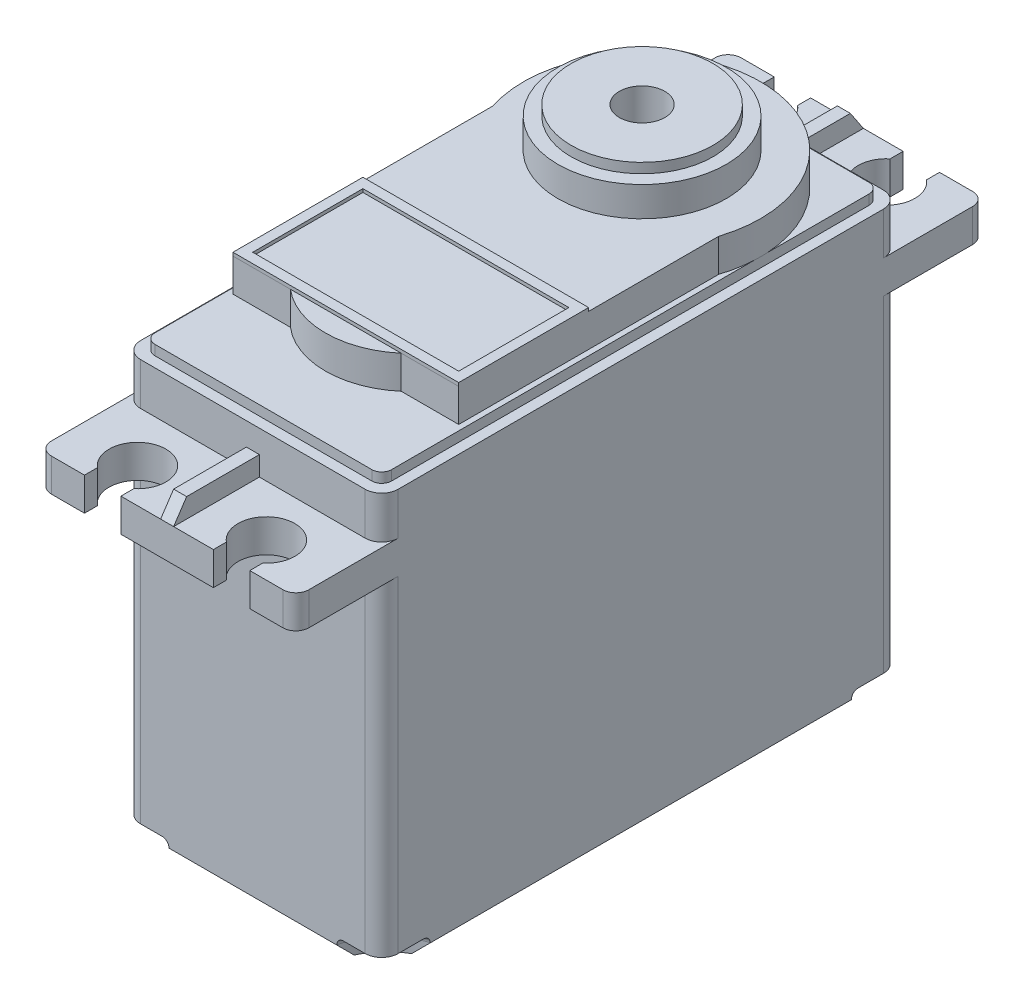
SolidWorks part; units mm, degrees
material "PBT General Purpose"
ref_plane "Front Plane" through (0, 0, 0) normal (0, 0, 1) x (1, 0, 0)
ref_plane "Top Plane" through (0, 0, 0) normal (0, 1, 0) x (1, 0, 0)
ref_plane "Right Plane" through (0, 0, 0) normal (1, 0, 0) x (0, 0, -1)
sketch "Sketch1" plane through (0, 0, 0) normal (0, 1, 0) x (1, 0, 0)
  line L0 (0, 19.94) -> (0, -19.94) construction
  line L1 (9.91, -19.94) -> (-9.91, -19.94)
  line L2 (9.91, -19.94) -> (9.91, 19.94)
  line L3 (9.91, 19.94) -> (-9.91, 19.94)
  line L4 (-9.91, -19.94) -> (-9.91, 19.94)
  line L5 (-9.91, 0) -> (9.91, 0) construction
  point P0 (0, 0)
  dimension "D1" = 19.82
  dimension "D2" = 39.88
extrude "Boss-Extrude1" add sketch "Sketch1" along normal blind 36.02
ref_plane "Plane1" through (0, 26.67, 0) normal (0, 1, 0) x (1, 0, 0)
sketch "Sketch2" plane through (0, 26.67, 0) normal (0, 1, 0) x (1, 0, 0)
  line L0 (0, 19.94) -> (0, -19.94) construction
  line L1 (9.91, 19.94) -> (-9.91, 19.94) construction
  line L2 (-9.91, -19.94) -> (9.91, -19.94) construction
  line L3 (-9.91, 0) -> (9.91, 0) construction
  line L4 (-9.91, 19.94) -> (-9.91, -19.94) construction
  line L5 (9.91, -19.94) -> (9.91, 19.94) construction
  line L7 (-9.91, 19.94) -> (9.91, 19.94)
  line L8 (-9.91, 19.94) -> (-9.91, 26.54)
  line L9 (-9.91, 26.54) -> (9.91, 26.54)
  line L10 (9.91, 19.94) -> (9.91, 26.54)
  line L11 (-9.91, -19.94) -> (9.91, -19.94)
  line L12 (-9.91, -19.94) -> (-9.91, -26.54)
  line L13 (-9.91, -26.54) -> (9.91, -26.54)
  line L14 (9.91, -19.94) -> (9.91, -26.54)
  dimension "D1" = 6.6
extrude "Boss-Extrude2" add sketch "Sketch2" along normal blind 2.54
ref_plane "Plane2" through (0, 29.21, 0) normal (0, 1, 0) x (1, 0, 0)
sketch "Sketch3" plane through (0, 29.21, 0) normal (0, 1, 0) x (1, 0, 0)
  line L0 (0, 26.54) -> (0, -26.54) construction
  line L1 (9.91, 26.54) -> (-9.91, 26.54) construction
  line L2 (-9.91, -26.54) -> (9.91, -26.54) construction
  line L3 (-4.96, 26.54) -> (-4.96, -26.54) construction
  line L4 (-6.36, 26.54) -> (-3.56, 26.54)
  line L5 (-6.36, 26.54) -> (-6.36, 25.54)
  line L6 (-3.56, 26.54) -> (-3.56, 25.54)
  line L7 (3.56, 26.54) -> (3.56, 25.54)
  line L8 (6.36, 26.54) -> (6.36, 25.54)
  line L9 (6.36, 26.54) -> (3.56, 26.54)
  arc A0 (-6.36, 25.5441) -> (-3.56, 25.5441) centre (-4.96, 23.86) ccw
  arc A1 (6.36, 25.5441) -> (3.56, 25.5441) centre (4.96, 23.86) cw
  point P11 (-4.96, 26.54)
  point P24 (4.96, 26.54)
  dimension "D5" = 2.19
  dimension "D1" = 4.96
  dimension "D2" = 2.8
  dimension "D3" = 1
  dimension "D4" = 23.86
extrude "Cut-Extrude1" cut sketch "Sketch3" along direction (0, -1, 0) on the side against the normal blind 2.54
mirror "Mirror1" about plane through (0, 0, 0) normal (0, 0, 1) of "Cut-Extrude1"
ref_plane "Plane3" through (0, 29.21, 0) normal (0, 1, 0) x (1, 0, 0)
sketch "Sketch4" plane through (0, 29.21, 0) normal (0, 1, 0) x (1, 0, 0)
  line L0 (0, 26.54) -> (0, -26.54) construction
  line L1 (3.56, 26.54) -> (-3.56, 26.54) construction
  line L2 (-3.56, -26.54) -> (3.56, -26.54) construction
  line L3 (-9.91, 0) -> (9.91, 0) construction
  line L4 (-9.91, 19.94) -> (-9.91, -19.94) construction
  line L5 (9.91, -19.94) -> (9.91, 19.94) construction
  line L6 (-9.91, 19.94) -> (9.91, 19.94) construction
  line L7 (-0.5, 26.54) -> (0.5, 26.54)
  line L8 (-0.5, 26.54) -> (-0.5, 19.94)
  line L9 (-0.5, 19.94) -> (0.5, 19.94)
  line L10 (0.5, 26.54) -> (0.5, 19.94)
  line L11 (0.5, -26.54) -> (0.5, -19.94)
  line L12 (-0.5, -19.94) -> (0.5, -19.94)
  line L13 (-0.5, -26.54) -> (-0.5, -19.94)
  line L14 (-0.5, -26.54) -> (0.5, -26.54)
  point P18 (0, 26.54)
  dimension "D1" = 1
extrude "Boss-Extrude3" add sketch "Sketch4" along normal blind 1.5
ref_plane "Plane4" through (-0.5, 0, 0) normal (-1, 0, 0) x (0, 0, 1)
sketch "Sketch5" plane through (-0.5, 0, 0) normal (-1, 0, 0) x (0, 0, 1)
  line L0 (0, 36.02) -> (0, 0) construction
  line L1 (-19.94, 36.02) -> (19.94, 36.02) construction
  line L2 (-26.54, 30.71) -> (-25.54, 30.71)
  line L3 (-26.54, 30.71) -> (-19.94, 30.71) construction
  line L4 (-26.54, 30.71) -> (-26.54, 29.21)
  line L5 (-25.54, 30.71) -> (-26.54, 29.21)
  line L6 (25.54, 30.71) -> (26.54, 29.21)
  line L7 (26.54, 30.71) -> (26.54, 29.21)
  line L8 (26.54, 30.71) -> (25.54, 30.71)
  dimension "D1" = 1
extrude "Cut-Extrude2" cut sketch "Sketch5" against normal through all both and the other way through all
ref_plane "Plane5" through (0, 36.02, 0) normal (0, 1, 0) x (1, 0, 0)
sketch "Sketch6" plane through (0, 36.02, 0) normal (0, 1, 0) x (1, 0, 0)
  line L1 (-9.91, 19.94) -> (9.91, 19.94)
  line L2 (-9.91, 19.94) -> (-9.91, -19.94)
  line L3 (-9.91, -19.94) -> (9.91, -19.94)
  line L4 (9.91, 19.94) -> (9.91, -19.94)
extrude "Cut-Extrude3" cut sketch "Sketch6" against normal blind 3.55
ref_plane "Plane6" through (0, 32.47, 0) normal (0, 1, 0) x (1, 0, 0)
sketch "Sketch7" plane through (0, 32.47, 0) normal (0, 1, 0) x (1, 0, 0)
  line L0 (0, 19.94) -> (0, -19.94) construction
  line L5 (-9.91, 0) -> (9.91, 0) construction
  line L18 (-9.11, 19.136) -> (-9.11, -19.136)
  line L19 (9.11, 19.136) -> (9.11, -19.136)
  line L20 (-9.11, 19.136) -> (9.11, 19.136)
  line L21 (-9.11, -19.136) -> (9.11, -19.136)
  line L22 (-0.5, -19.94) -> (-9.91, -19.94) construction
  line L23 (-9.91, 19.94) -> (-0.5, 19.94) construction
  line L24 (-9.91, 19.94) -> (-9.91, -19.94) construction
  point P7 (-9.11, 0)
  point P10 (9.11, 0)
  dimension "D1" = 18.22
  dimension "D2" = 0.804
  dimension "D3" = 0.804
  dimension "D4" = 0.8
extrude "Boss-Extrude4" add sketch "Sketch7" along normal blind 0.762
fillet "Fillet1" radius 1.27 8 edges at (-9.91, 30.84, 19.94) (-9.91, 13.335, 19.94) (-9.91, 30.84, -19.94) (-9.91, 13.335, -19.94) (9.91, 30.84, -19.94) (9.91, 13.335, -19.94) (9.91, 30.84, 19.94) (9.91, 13.335, 19.94)
fillet "Fillet2" radius 0.762 4 edges at (-9.11, 32.851, -19.136) (9.11, 32.851, -19.136) (9.11, 32.851, 19.136) (-9.11, 32.851, 19.136)
ref_plane "Plane7" through (0, 33.232, 0) normal (0, 1, 0) x (1, 0, 0)
sketch "Sketch8" plane through (0, 33.232, 0) normal (0, 1, 0) x (1, 0, 0)
  line L0 (0, 19.136) -> (0, -19.136) construction
  line L1 (8.348, 19.136) -> (-8.348, 19.136) construction
  line L2 (-8.348, -19.136) -> (8.348, -19.136) construction
  line L3 (-8.6857, -12.786) -> (8.6857, -12.786)
  line L4 (-8.6857, -12.786) -> (-8.6857, 7.214)
  line L5 (8.6857, -12.786) -> (8.6857, 7.214)
  arc A0 (8.6857, 7.214) -> (-8.6857, 7.214) centre (0, 10.011) ccw
  point P9 (0, -12.786)
  dimension "D3" = 18.25
  dimension "D1" = 6.35
  dimension "D2" = 20
extrude "Boss-Extrude5" add sketch "Sketch8" along normal blind 2.54
ref_plane "Plane8" through (0, 35.772, 0) normal (0, 1, 0) x (1, 0, 0)
sketch "Sketch9" plane through (0, 35.772, 0) normal (0, 1, 0) x (1, 0, 0)
  line L0 (0, 19.136) -> (0, -12.786) construction
  line L1 (8.348, 19.136) -> (-8.348, 19.136) construction
  line L2 (-8.6857, -12.786) -> (8.6857, -12.786) construction
  circle A0 centre (0, 10.011) radius 6.475
  arc A1 (0, 19.136) -> (-9.11, 10.534) centre (0, 10.011) ccw construction
  dimension "D1" = 12.95
extrude "Boss-Extrude6" add sketch "Sketch9" along normal blind 2.286
sketch "Sketch10" plane through (0, 38.058, 0) normal (0, 1, 0) x (1, 0, 0)
  circle A0 centre (0, 10.011) radius 5.46
  dimension "D1" = 10.92
extrude "Boss-Extrude7" add sketch "Sketch10" along normal blind 0.762
sketch "Sketch11" plane through (0, 38.82, 0) normal (0, 1, 0) x (1, 0, 0)
  circle A0 centre (0, 10.011) radius 1.75
  dimension "D1" = 3.5
extrude "Cut-Extrude4" cut sketch "Sketch11" against normal blind 2.54
sketch "Sketch12" plane through (0, 35.772, 0) normal (0, 1, 0) x (1, 0, 0)
  line L0 (-8.6857, -2.789) -> (8.6857, -2.789)
  line L1 (-8.6857, 7.214) -> (-8.6857, -12.786) construction
  line L2 (8.6857, -12.786) -> (8.6857, 7.214) construction
  line L3 (-8.6857, -2.789) -> (-8.6857, -12.789)
  line L4 (-8.6857, 7.214) -> (-8.6857, -12.786) construction
  line L5 (-8.6857, -12.789) -> (8.6857, -12.789)
  line L6 (8.6857, -12.789) -> (8.6857, -2.789)
  line L7 (-7.9257, -3.549) -> (-7.9257, -12.029)
  line L8 (-7.9257, -12.029) -> (7.9257, -12.029)
  line L9 (7.9257, -12.029) -> (7.9257, -3.549)
  line L10 (-7.9257, -3.549) -> (7.9257, -3.549)
  line L11 (0, -2.789) -> (0, -12.789) construction
  line L12 (8.6857, -7.789) -> (-7.9257, -7.789) construction
  circle A0 centre (0, 10.011) radius 1.75 construction
  dimension "D1" = 12.8
  dimension "D2" = 10
  dimension "D3" = 0.76
extrude "Boss-Extrude8" add sketch "Sketch12" along normal blind 0.254
ref_plane "Plane9" through (0, 33.232, 0) normal (0, 1, 0) x (1, 0, 0)
sketch "Sketch13" plane through (0, 33.232, 0) normal (0, 1, 0) x (1, 0, 0)
  line L0 (-7.9257, -7.789) -> (7.9257, -7.789) construction
  line L1 (-7.9257, -3.549) -> (-7.9257, -12.029) construction
  line L2 (7.9257, -12.029) -> (7.9257, -3.549) construction
  line L3 (0, -12.029) -> (0, -19.136) construction
  line L5 (-8.348, -19.136) -> (8.348, -19.136) construction
  line L6 (-4.2608, -12.79) -> (4.2608, -12.79)
  arc A0 (-4.2608, -12.79) -> (4.2608, -12.79) centre (0, -7.789) ccw
  point P18 (0, -12.029)
  dimension "D2" = 13.14
  dimension "D1" = 12.79
extrude "Boss-Extrude9" add sketch "Sketch13" along normal blind 2.54
ref_plane "Plane10" through (0, 0, 0) normal (0, -1, 0) x (-1, 0, 0)
sketch "Sketch14" plane through (0, 0, 0) normal (0, -1, 0) x (1, 0, 0)
  line L0 (0, -19.94) -> (0, 19.94) construction
  line L3 (9.91, 0) -> (-9.91, 0) construction
  line L9 (6.4637, -19.94) -> (9.91, -19.94)
  line L10 (9.91, -19.94) -> (9.91, -16.2118)
  line L11 (-9.91, -19.94) -> (-9.91, -16.2118)
  line L12 (-6.4637, -19.94) -> (-9.91, -19.94)
  line L13 (-6.4637, 19.94) -> (-9.91, 19.94)
  line L14 (-9.91, 19.94) -> (-9.91, 16.2118)
  line L15 (9.91, 19.94) -> (9.91, 16.2118)
  line L16 (6.4637, 19.94) -> (9.91, 19.94)
  line L17 (8.64, 19.94) -> (-8.64, 19.94) construction
  line L18 (9.91, 18.67) -> (9.91, -18.67) construction
  line L19 (-9.91, -18.67) -> (-9.91, 18.67) construction
  line L20 (8.64, -19.94) -> (-8.64, -19.94) construction
  arc A0 (9.91, -16.2118) -> (6.4637, -19.94) centre (11.35, -21) ccw
  arc A1 (-9.91, -16.2118) -> (-6.4637, -19.94) centre (-11.35, -21) cw
  arc A2 (-9.91, 16.2118) -> (-6.4637, 19.94) centre (-11.35, 21) ccw
  arc A3 (9.91, 16.2118) -> (6.4637, 19.94) centre (11.35, 21) cw
  dimension "D3" = 5
  dimension "D1" = 3.4463
  dimension "D2" = 3.7282
extrude "Cut-Extrude5" cut sketch "Sketch14" against normal blind 1.524
sketch "Sketch15" plane through (0, 0, 0) normal (0, -1, 0) x (-1, 0, 0)
  circle A0 centre (-8.64, 18.67) radius 0.5
  arc A1 (-8.64, 19.94) -> (-9.91, 18.67) centre (-8.64, 18.67) ccw construction
  circle A2 centre (8.64, 18.67) radius 0.5
  circle A3 centre (8.64, -18.67) radius 0.5
  circle A4 centre (-8.64, -18.67) radius 0.5
  arc A5 (-9.91, -18.67) -> (-8.64, -19.94) centre (-8.64, -18.67) ccw construction
  arc A6 (8.64, -19.94) -> (9.91, -18.67) centre (8.64, -18.67) ccw construction
  arc A7 (9.91, 18.67) -> (8.64, 19.94) centre (8.64, 18.67) ccw construction
  dimension "D1" = 1
extrude "Cut-Extrude6" cut sketch "Sketch15" against normal blind 6
chamfer "Chamfer1" distance 1 angle 45 4 edges at (0, 0, 19.94) (0, 0, -19.94) (-9.91, 0, 0) (9.91, 0, 0)
fillet "Fillet3" radius 0.5 4 edges at (7.6784, 1.524, -17.606) (-7.6784, 1.524, -17.606) (7.6784, 1.524, 17.606) (-7.6784, 1.524, 17.606)
ref_plane "Plane11" through (0, 0, -19.94) normal (0, 0, -1) x (-1, 0, 0)
sketch "Sketch16" plane through (0, 0, -19.94) normal (0, 0, -1) x (-1, 0, 0)
  line L0 (0, 26.67) -> (0, 0) construction
  line L1 (8.64, 26.67) -> (-8.64, 26.67) construction
  line L2 (-6.4637, 1) -> (6.4637, 1) construction
  line L3 (-3.175, 1) -> (3.175, 1)
  line L4 (-3.175, 1) -> (-3.175, 4.6868)
  line L5 (-3.175, 4.6868) -> (3.175, 4.6868)
  line L6 (3.175, 1) -> (3.175, 4.6868)
  line L7 (-2.675, 1.5) -> (-2.675, 4.1868)
  line L8 (-2.675, 4.1868) -> (2.675, 4.1868)
  line L9 (2.675, 1.5) -> (2.675, 4.1868)
  line L10 (-2.675, 1.5) -> (2.675, 1.5)
  point P11 (0, 4.6868)
  dimension "D1" = 3.175
  dimension "D2" = 0.5
extrude "Boss-Extrude10" add sketch "Sketch16" along normal blind 1.5
fillet "Fillet4" radius 0.5 4 edges at (3.175, 4.6868, -20.69) (3.175, 1, -20.69) (-3.175, 1, -20.69) (-3.175, 4.6868, -20.69)
fillet "Fillet5" radius 1 4 edges at (9.91, 27.94, 26.54) (-9.91, 27.94, 26.54) (9.91, 27.94, -26.54) (-9.91, 27.94, -26.54)
